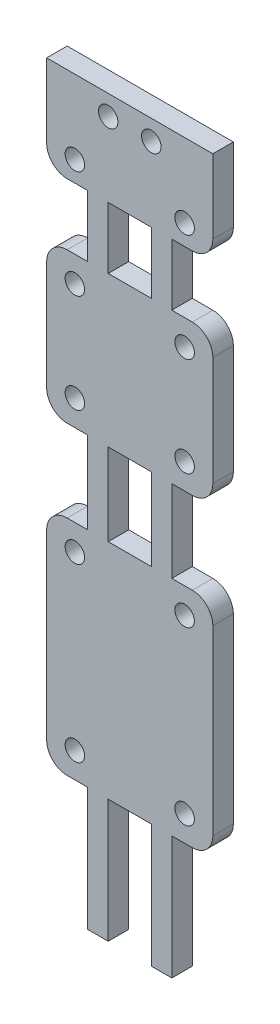
SolidWorks part; units mm, degrees
ref_plane "Front Plane" through (0, 0, 0) normal (0, 0, 1) x (1, 0, 0)
ref_plane "Top Plane" through (0, 0, 0) normal (0, 1, 0) x (1, 0, 0)
ref_plane "Right Plane" through (0, 0, 0) normal (1, 0, 0) x (0, 0, -1)
sketch "Sketch1" plane through (0, 0, 0) normal (0, 0, 1) x (1, 0, 0)
  line L0 (0, 1.5) -> (0, 14) construction
  line L1 (16.2, 1.5) -> (16.2, 14) construction
  line L2 (2, 47.74) -> (4, 47.74)
  line L3 (0, 1.5) -> (16.2, 1.5) construction
  line L4 (0, 14) -> (4, 14) construction
  line L5 (2, 26) -> (4, 26)
  line L6 (16.2, 85.59) -> (0, 85.59)
  line L7 (2, 70.385) -> (4, 70.385)
  line L8 (2, 55.74) -> (4, 55.74)
  line L9 (0, 28) -> (0, 45.74)
  line L10 (2, 76.385) -> (4, 76.385)
  line L11 (16.2, 28) -> (16.2, 45.74)
  line L12 (16.2, 57.74) -> (16.2, 68.385)
  line L13 (0, 57.74) -> (0, 68.385)
  line L14 (16.2, 78.385) -> (16.2, 85.59)
  line L15 (0, 78.385) -> (0, 85.59)
  line L16 (6, 70.385) -> (6, 76.385)
  line L17 (4, 55.74) -> (4, 47.74)
  line L18 (4, 70.385) -> (4, 76.385)
  line L19 (6, 55.74) -> (6, 47.74)
  line L20 (4, 26) -> (4, 14)
  line L21 (6, 26) -> (6, 14)
  line L22 (8.1, 1.5) -> (8.1, 85.59) construction
  line L23 (10.2, 26) -> (10.2, 14)
  line L24 (12.2, 26) -> (12.2, 14)
  line L25 (10.2, 55.74) -> (10.2, 47.74)
  line L26 (12.2, 55.74) -> (12.2, 47.74)
  line L27 (10.2, 70.385) -> (10.2, 76.385)
  line L28 (12.2, 70.385) -> (12.2, 76.385)
  line L29 (6, 26) -> (10.2, 26)
  line L30 (6, 14) -> (10.2, 14) construction
  line L31 (12.2, 14) -> (16.2, 14) construction
  line L32 (12.2, 26) -> (14.2, 26)
  line L33 (12.2, 47.74) -> (14.2, 47.74)
  line L34 (6, 47.74) -> (10.2, 47.74)
  line L35 (12.2, 76.385) -> (14.2, 76.385)
  line L36 (6, 76.385) -> (10.2, 76.385)
  line L37 (6, 70.385) -> (10.2, 70.385)
  line L38 (12.2, 70.385) -> (14.2, 70.385)
  line L39 (12.2, 55.74) -> (14.2, 55.74)
  line L40 (6, 55.74) -> (10.2, 55.74)
  line L41 (4, 14) -> (6, 14)
  line L42 (10.2, 14) -> (12.2, 14)
  circle A0 centre (13.45, 45.24) radius 0.95
  circle A1 centre (2.75, 67.885) radius 0.95
  circle A2 centre (13.45, 58.24) radius 0.95
  circle A3 centre (13.45, 78.385) radius 0.95
  circle A4 centre (2.75, 28.5) radius 0.95
  circle A5 centre (2.75, 78.385) radius 0.95
  circle A6 centre (2.75, 58.24) radius 0.95
  circle A7 centre (2.85, 11.5) radius 0.95 construction
  circle A8 centre (13.35, 11.5) radius 0.95 construction
  circle A9 centre (13.35, 5.5) radius 0.95 construction
  circle A10 centre (2.85, 5.5) radius 0.95 construction
  circle A11 centre (6, 83.635) radius 0.95
  circle A12 centre (13.45, 28.5) radius 0.95
  circle A13 centre (13.45, 67.885) radius 0.95
  circle A14 centre (10.2, 83.635) radius 0.95
  circle A15 centre (2.75, 45.24) radius 0.95
  arc A16 (0, 28) -> (2, 26) centre (2, 28) ccw
  arc A17 (16.2, 28) -> (14.2, 26) centre (14.2, 28) cw
  arc A18 (16.2, 45.74) -> (14.2, 47.74) centre (14.2, 45.74) ccw
  arc A19 (0, 45.74) -> (2, 47.74) centre (2, 45.74) cw
  arc A20 (0, 57.74) -> (2, 55.74) centre (2, 57.74) ccw
  arc A21 (16.2, 57.74) -> (14.2, 55.74) centre (14.2, 57.74) cw
  arc A22 (0, 68.385) -> (2, 70.385) centre (2, 68.385) cw
  arc A23 (16.2, 68.385) -> (14.2, 70.385) centre (14.2, 68.385) ccw
  arc A24 (16.2, 78.385) -> (14.2, 76.385) centre (14.2, 78.385) cw
  arc A25 (2, 76.385) -> (0, 78.385) centre (2, 78.385) cw
  point P77 (0, 26)
  point P80 (16.2, 26)
  point P83 (16.2, 47.74)
  point P86 (0, 47.74)
  point P89 (0, 55.74)
  point P92 (16.2, 55.74)
  point P95 (0, 70.385)
  point P98 (16.2, 70.385)
  point P101 (16.2, 76.385)
  point P104 (0, 76.385)
  dimension "D1" = 4
  dimension "D40" = 2
  dimension "D41" = 1.9
  dimension "D2" = 4
  dimension "D3" = 6
  dimension "D4" = 6
  dimension "D5" = 2.5
  dimension "D6" = 12
  dimension "D7" = 2.85
  dimension "D8" = 2.85
  dimension "D9" = 2.85
  dimension "D10" = 16.2
  dimension "D11" = 21.74
  dimension "D12" = 2.75
  dimension "D13" = 2.75
  dimension "D14" = 2.75
  dimension "D15" = 2.75
  dimension "D16" = 2.5
  dimension "D17" = 2.5
  dimension "D18" = 2.5
  dimension "D19" = 2.5
  dimension "D20" = 8
  dimension "D21" = 14.645
  dimension "D22" = 2.75
  dimension "D23" = 2.75
  dimension "D24" = 2.5
  dimension "D25" = 2.5
  dimension "D26" = 2.5
  dimension "D27" = 2.5
  dimension "D28" = 2.75
  dimension "D29" = 2.75
  dimension "D30" = 6
  dimension "D31" = 9.205
  dimension "D32" = 2.75
  dimension "D33" = 6
  dimension "D34" = 2
  dimension "D35" = 7.25
  dimension "D36" = 2
  dimension "D37" = 7.25
  dimension "D38" = 6
  dimension "D39" = 2.75
extrude "Boss-Extrude1" add sketch "Sketch1" along normal blind 2
sketch "Sketch2" plane through (0, 0, 2) normal (0, 0, 1) x (1, 0, 0)
  line L0 (4, 76.385) -> (12.2, 76.385)
  line L1 (12.2, 76.385) -> (12.2, 70.385)
  line L2 (12.2, 70.385) -> (4, 70.385)
  line L3 (4, 70.385) -> (4, 76.385)
  line L4 (4, 55.74) -> (12.2, 55.74)
  line L5 (12.2, 55.74) -> (12.2, 47.74)
  line L6 (12.2, 47.74) -> (4, 47.74)
  line L7 (4, 47.74) -> (4, 55.74)
  line L8 (4, 26) -> (12.2, 26)
  line L9 (12.2, 26) -> (12.2, 14)
  line L10 (12.2, 14) -> (4, 14)
  line L11 (4, 14) -> (4, 26)
extrude "Cut-Extrude1" [suppressed] cut sketch "Sketch2" against normal up to surface (2 mm away)
equation "\"D11@Sketch1\"= \"HL@parametersSketch@prostheticParameters.SLDPRT\" * 0.204 - 4 - 12 'Pinky PIP Length"
equation "\"D21@Sketch1\"= \"HL@parametersSketch@prostheticParameters.SLDPRT\" * 0.117 - 4 - 3 'Pinky MIP Length"
equation "\"D31@Sketch1\"= \"HL@parametersSketch@prostheticParameters.SLDPRT\" * 0.093 - 3 - 5'Pinky DIP Length"
equation "\"D10@Sketch1\"= \"fingerWidth@parametersSketch@prostheticParameters.SLDPRT\"'Pinky Width"
equation "\"D41@Sketch1\"= 1.5 + \"tol1@parametersSketch@prostheticParameters.SLDPRT\""
